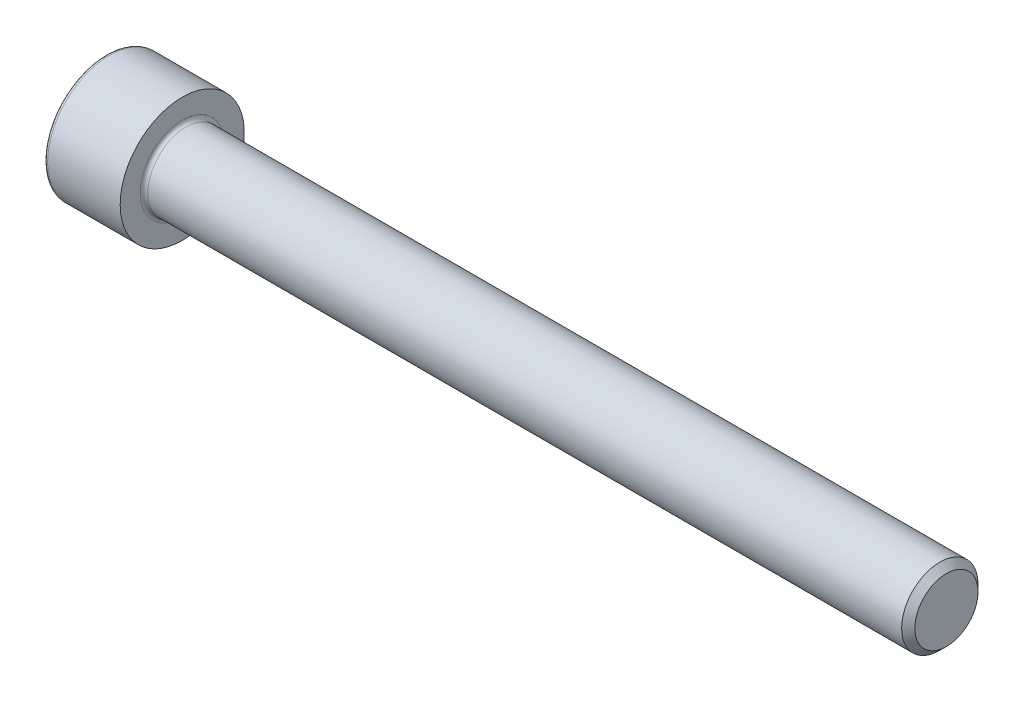
SolidWorks part; units mm, degrees
revolve "Base-Revolve" add sketch "BodySke"
sketch "BodySke" plane through (0, 0, 0) normal (0, 0, 1) x (1, 0, 0)
  line L0 (0, 0) -> (0, 6.5)
  line L1 (0, 6.5) -> (8, 6.5)
  line L2 (8, 6.5) -> (8, 4)
  line L3 (8, 4) -> (87.3095, 4)
  line L4 (88, 3.3095) -> (88, 0)
  line L5 (88, 0) -> (0, 0)
  line L6 (-31.75, 0) -> (127, 0) construction
  line L8 (88, 3.3095) -> (87.3095, 4)
  line L10 (88, -3.3095) -> (87.3095, -4) construction
  line L11 (9.25, 9.525) -> (9.25, 3.175) construction
  line L12 (60, 9.525) -> (60, 3.175) construction
  line L13 (28, 9.525) -> (28, 3.175) construction
  dimension "Head_ht" = 8
  dimension "Body_ch_ang" = 45
  dimension "Diameter" = 8
  dimension "Minor_dia" = 6.619
  dimension "Advance" = 1.25
  dimension "Thread_length" = 60
  dimension "Head_dia" = 13
cosmetic thread "ThreadCosmetic" [suppressed]
fillet "Fillet1" radius 0.4 1 edges at (8, 0, 4)
fillet "Fillet2" radius 0.4 1 edges at (0, 0, 6.5)
ref_plane "Plane1" through (0, 0, 0) normal (0, 0, 1) x (1, 0, 0)
ref_plane "Plane2" through (0, 0, 0) normal (0, 1, 0) x (1, 0, 0)
ref_plane "Plane3" through (0, 0, 0) normal (1, 0, 0) x (0, 0, -1)
sketch "Sketch2" plane through (0, 0, 0) normal (0, 0, 1) x (1, 0, 0)
  line L0 (0, 3.0475) -> (4, 3.0475)
  line L1 (4, 3.0475) -> (5.7595, 0)
  line L2 (-31.75, 0) -> (127, 0) construction
  line L3 (5.7595, 0) -> (0, 0)
  line L4 (0, 0) -> (0, 3.0475)
  line L6 (0, 0) -> (47.625, 0) construction
  dimension "D1" = 3.0475
  dimension "D2" = 60
  dimension "Depth" = 4
revolve "Hex-PreBroach" cut sketch "Sketch2" angle 360 about L6
sketch "Sketch3" plane through (0, 0, 0) normal (-1, 0, 0) x (0, 0.5, 0.866)
  line L0 (1.7595, 3.0475) -> (-1.7595, 3.0475)
  line L1 (-1.7595, 3.0475) -> (-3.5189, 0)
  line L2 (1.7595, 3.0475) -> (3.5189, 0)
  line L3 (1.7595, -3.0475) -> (3.5189, 0)
  line L4 (1.7595, -3.0475) -> (-1.7595, -3.0475)
  line L5 (-1.7595, -3.0475) -> (-3.5189, 0)
  dimension "D1" = 3.0475
  dimension "D2" = 3.0475
  dimension "Hex_size" = 6.095
extrude "Hex" cut sketch "Sketch3" against normal blind 4
sketch "ThdSchSke" plane through (0, 0, 0) normal (0, 0, 1) x (1, 0, 0)
  line L0 (60, -3.3095) -> (59.5165, -4)
  line L1 (60, -3.3095) -> (60.4835, -4)
  line L2 (60.4835, -4) -> (60.4835, -5)
  line L3 (-3.175, 0) -> (5.1513, 0) construction
  line L4 (0, 6.1) -> (0, -6.1) construction
  line L5 (60.4835, -5) -> (59.5165, -5)
  line L6 (59.5165, -5) -> (59.5165, -4)
  dimension "Thread_minor" = 6.619
  dimension "Diameter" = 8
revolve "ThreadSchematic" [suppressed] cut sketch "ThdSchSke" angle 360 about L3
pattern_linear "ThdSchPat" [suppressed]
equation "\"D2@Sketch3\" = \"Hex_size@Sketch3\" / 2"
equation "\"D1@Sketch3\" = \"Hex_size@Sketch3\" / 2"
equation "\"D1@Sketch2\" = \"Hex_size@Sketch3\" / 2"
equation "\"Thread_minor@ThreadCosmetic\"  =  \"Minor_dia@BodySke\""
equation "\"Depth@Sketch2\" =  \"Key_eng@Hex\""
equation "\"Thread_length@ThreadCosmetic\" = ((sgn( (\"Length@BodySke\" - \"Advance@BodySke\" * 3.0) - \"Thread_nom@BodySke\" )-1)*( (\"Length@BodySke\" - \"Advance@BodySke\" * 3.0) - \"Thread_nom@BodySke\" ))/-2+ \"Thread_nom@BodySke\""
equation "\"Thread_minor@ThdSchSke\" = \"Minor_dia@BodySke\""
equation "\"Diameter@ThdSchSke\" = \"Diameter@BodySke\""
equation "\"Overcut@ThdSchSke\" = \"Diameter@BodySke\" * 1.25"
equation "\"Start@ThdSchSke\" = \"Head_ht@BodySke\" + \"Length@BodySke\" - \"Thread_length@ThreadCosmetic\"  '---Non-countersunk---"
equation "\"Num_threads@ThdSchPat\" = int( \"Thread_length@ThreadCosmetic\" / \"Advance@BodySke\" + 0.999 )  + 1"
equation "\"Advance@ThdSchPat\" = \"Thread_length@ThreadCosmetic\" /  (\"Num_threads@ThdSchPat\" - 1) 'relax it"
equation "\"Num_threads@ThdSchPat\" = \"Num_threads@ThdSchPat\" - sgn( \"Num_threads@ThdSchPat\" - 1) '---chamfered tips only---"
